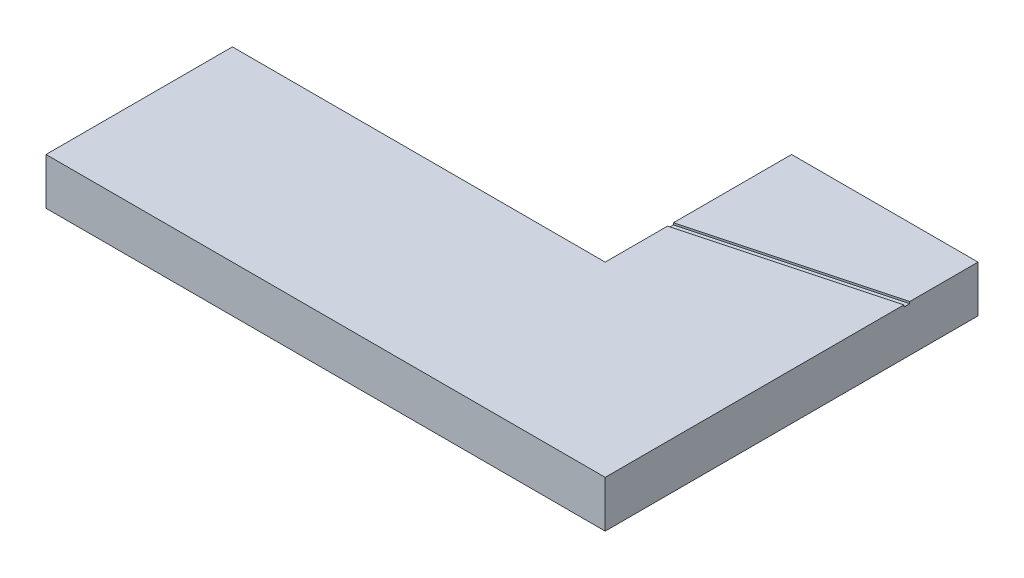
SolidWorks part; units mm, degrees
ref_plane "Front Plane" through (0, 0, 0) normal (0, 0, 1) x (1, 0, 0)
ref_plane "Top Plane" through (0, 0, 0) normal (0, 1, 0) x (1, 0, 0)
ref_plane "Right Plane" through (0, 0, 0) normal (1, 0, 0) x (0, 0, -1)
sketch "Sketch1" plane through (0, 0, 0) normal (0, 1, 0) x (1, 0, 0)
  line L0 (0, 0) -> (0, 100)
  line L1 (0, 100) -> (100, 100)
  line L2 (100, 100) -> (100, -100)
  line L3 (100, -100) -> (-200, -100)
  line L4 (-200, -100) -> (-200, 0)
  line L5 (-200, 0) -> (0, 0)
  dimension "D1" = 300
  dimension "D2" = 200
  dimension "D3" = 100
  dimension "D4" = 200
extrude "Boss-Extrude1" add sketch "Sketch1" along normal blind 25
sketch "Sketch2" plane through (0, 25, 0) normal (0, 1, 0) x (1, 0, 0)
  line L0 (0, 100) -> (0, 0) construction
  line L1 (0, 0) -> (-200, 0) construction
  line L2 (0, 35) -> (100, 35) construction
  line L3 (100, -100) -> (100, 100) construction
  line L4 (0, 35) -> (100, 61.7949) construction
  line L5 (150.4142, 73.7504) -> (-91.0673, 9.0457)
  line L6 (150.4142, 73.7504) -> (149.6377, 76.6482)
  line L7 (-91.0673, 9.0457) -> (-91.8437, 11.9435)
  line L8 (149.6377, 76.6482) -> (-91.8437, 11.9435)
  line L9 (150.4142, 73.7504) -> (-91.8437, 11.9435) construction
  line L10 (-91.0673, 9.0457) -> (149.6377, 76.6482) construction
  line L11 (-91.4555, 10.4946) -> (150.026, 75.1993) construction
  point P0 (0, 35)
  point P11 (29.2852, 42.847)
  dimension "D1" = 35
  dimension "D2" = 15
  dimension "D3" = 3
  dimension "D4" = 250
extrude "Cut-Extrude1" cut sketch "Sketch2" against normal blind 1
sketch "Sketch3" plane through (0, 25, 0) normal (0, 1, 0) x (1, 0, 0)
  line L0 (0, 33.4471) -> (0, 36.5529)
  line L1 (0, 33.4471) -> (100, 60.242)
  line L2 (0, 36.5529) -> (100, 63.3478)
  line L3 (100, 60.242) -> (100, 63.3478)
  line L4 (0, 35) -> (100, 61.7949) construction
  line L5 (15, 39.0192) -> (-200, -85.1111) construction
  line L6 (-200, 0) -> (-200, -100) construction
  line L7 (15, 39.0192) -> (-200, 39.0192) construction
  line L8 (0, 100) -> (0, 36.5529) construction
  dimension "D1" = 15
  dimension "D2" = 30
